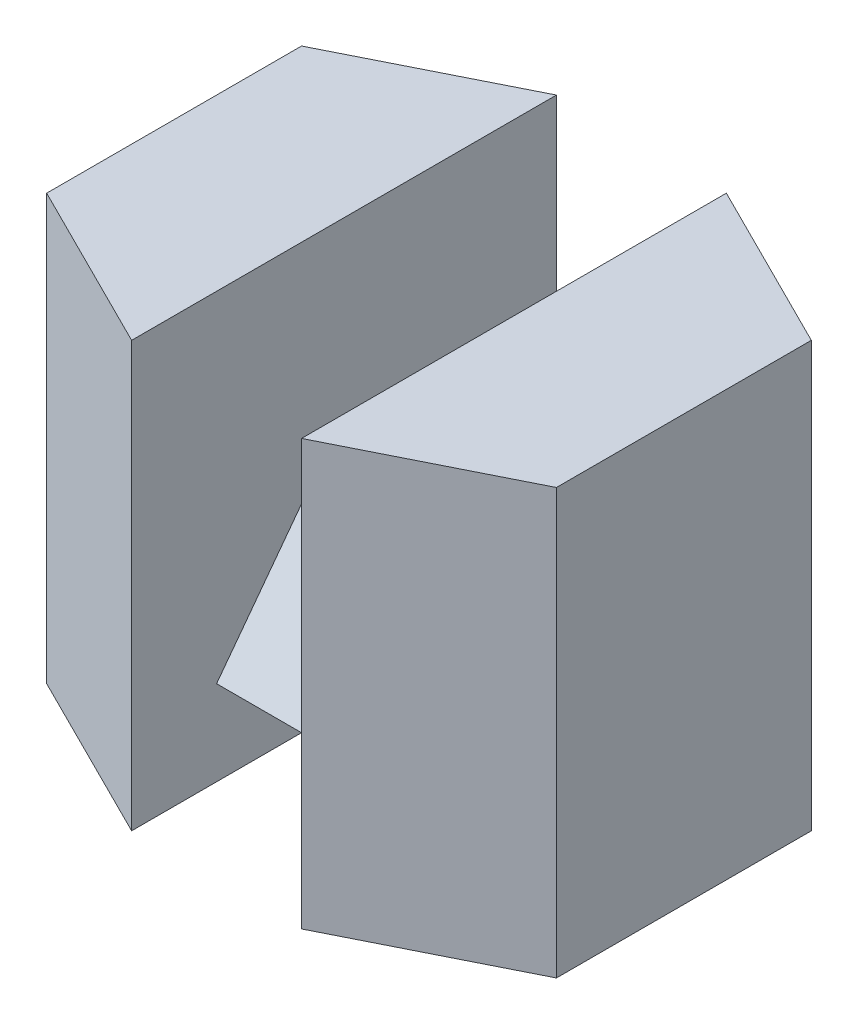
SolidWorks part; units mm, degrees
ref_plane "Front Plane" through (0, 0, 0) normal (0, 0, 1) x (1, 0, 0)
ref_plane "Top Plane" through (0, 0, 0) normal (0, 1, 0) x (1, 0, 0)
ref_plane "Right Plane" through (0, 0, 0) normal (1, 0, 0) x (0, 0, -1)
sketch "Sketch1" plane through (0, 0, 0) normal (0, 0, 1) x (1, 0, 0)
  line L1 (0, 0) -> (10, 0)
  line L2 (0, 0) -> (0, 25)
  line L3 (0, 25) -> (10, 25)
  line L4 (10, 0) -> (10, 25)
  dimension "D1" = 25
  dimension "D2" = 10
extrude "Boss-Extrude1" add sketch "Sketch1" along normal blind 25
sketch "Sketch2" plane through (0, 25, 0) normal (0, 1, 0) x (1, 0, 0)
  line L0 (0, 0) -> (10, 0)
  line L1 (10, 0) -> (10, -5)
  line L2 (10, -25) -> (10, 0) construction
  line L3 (10, -5) -> (0, 0)
  line L4 (0, -25) -> (10, -20)
  line L5 (10, -20) -> (10, -25)
  line L6 (10, -25) -> (0, -25)
  dimension "D1" = 5
  dimension "D2" = 5
extrude "Cut-Extrude1" cut sketch "Sketch2" against normal blind 25
sketch "Sketch3" plane through (0, 0, 0) normal (-1, 0, 0) x (0, 0, 1)
  line L0 (25, 0) -> (0, 0) construction
  line L1 (5, 5) -> (20, 5)
  line L2 (5, 5) -> (5, 15)
  line L3 (5, 15) -> (20, 15)
  line L4 (20, 5) -> (20, 15)
  line L5 (0, 25) -> (0, 0) construction
  dimension "D1" = 15
  dimension "D2" = 10
  dimension "D3" = 5
  dimension "D4" = 5
extrude "Boss-Extrude2" add sketch "Sketch3" along normal blind 10
sketch "Sketch4" plane through (-10, 0, 0) normal (-1, 0, 0) x (0, 0, 1)
  line L0 (5, 5) -> (12.5, 15)
  line L1 (20, 15) -> (5, 15) construction
  line L2 (12.5, 15) -> (20, 5)
  line L3 (20, 5) -> (20, 15)
  line L4 (20, 15) -> (12.5, 15)
  line L5 (5, 15) -> (5, 5)
  line M1 (5, 15) -> (5, 5)
  line M3 (20, 5) -> (20, 15)
  line M4 (20, 15) -> (5, 15)
extrude "Cut-Extrude2" cut sketch "Sketch4" against normal blind 10 contours L2 M4 M3 | L0 M1 M4
ref_plane "Plane1" through (-10, 0, 0) normal (-1, 0, 0) x (0, 0, 1)
sketch "Sketch5" plane through (-10, 0, 0) normal (-1, 0, 0) x (0, 0, 1)
  line L1 (0, 0) -> (25, 0)
  line L2 (0, 0) -> (0, 25)
  line L3 (0, 25) -> (25, 25)
  line L4 (25, 0) -> (25, 25)
extrude "Boss-Extrude3" add sketch "Sketch5" along normal blind 10
sketch "Sketch6" plane through (0, 25, 0) normal (0, 1, 0) x (1, 0, 0)
  line L0 (-10, 0) -> (-20, 0)
  line L1 (-10, 14.3362) -> (-10, -14.3362) construction
  line L2 (-20, 0) -> (-20, -5)
  line L3 (-20, -25) -> (-20, 0) construction
  line L4 (-20, -5) -> (-10, 0)
  line L5 (-20, -25) -> (-20, -20)
  line L6 (-20, -20) -> (-10, -25)
  line L7 (-20, -25) -> (-10, -25) construction
  line L8 (-10, -25) -> (-20, -25)
  dimension "D1" = 5
  dimension "D2" = 5
extrude "Cut-Extrude3" cut sketch "Sketch6" against normal blind 25
